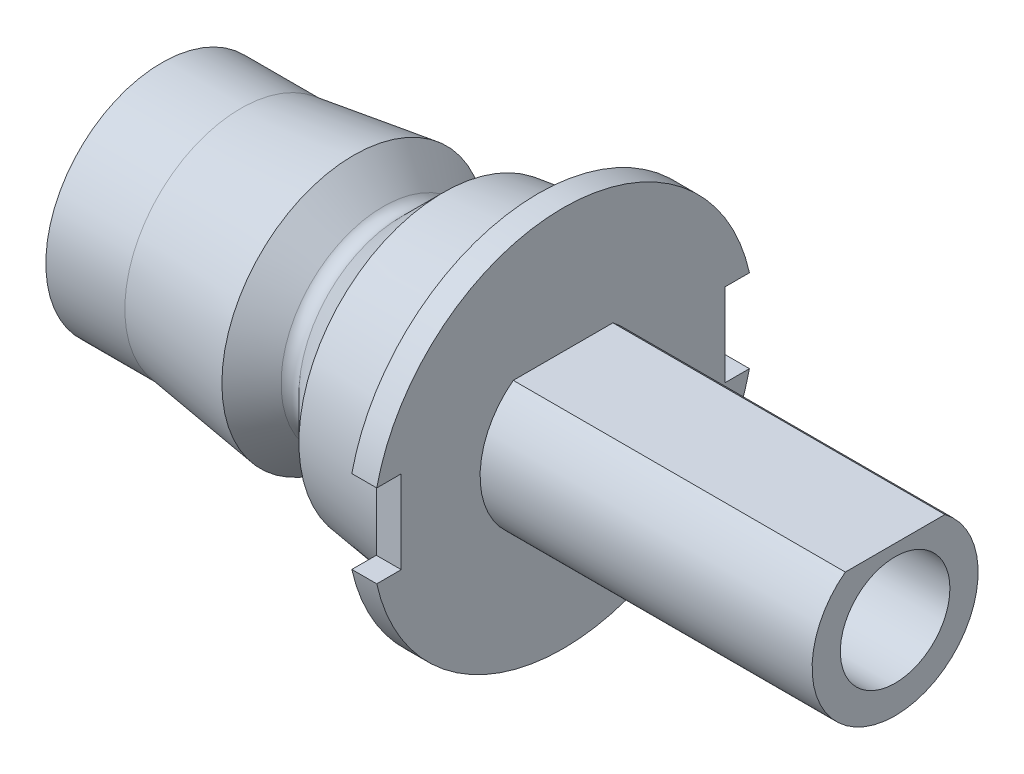
SolidWorks part; units mm, degrees
ref_plane "Front Plane" through (0, 0, 0) normal (0, 0, 1) x (1, 0, 0)
ref_plane "Top Plane" through (0, 0, 0) normal (0, 1, 0) x (1, 0, 0)
ref_plane "Right Plane" through (0, 0, 0) normal (1, 0, 0) x (0, 0, -1)
sketch "Sketch1" plane through (0, 0, 0) normal (0, 0, 1) x (1, 0, 0)
  line L0 (0, 0) -> (0, 6.982)
  line L1 (0, 6.982) -> (4.76, 6.982)
  line L2 (4.76, 6.982) -> (11.56, 7.9377)
  line L3 (11.56, 7.9377) -> (13.3431, 6.1545)
  line L4 (11.56, 7.9377) -> (23.1675, 9.569) construction
  line L5 (16.96, 8.6966) -> (22.6765, 9.5)
  line L6 (4.76, 6.982) -> (7.8351, 6.982) construction
  line L7 (11.56, 7.9377) -> (15.4875, 7.9377) construction
  line L8 (16.96, 8.6966) -> (14.4179, 6.1545)
  line L9 (16.96, 8.6966) -> (14.3792, 8.6966) construction
  line L10 (14.4179, 6.1545) -> (13.8805, 6.6919) construction
  line L11 (13.8805, 6.6919) -> (13.3431, 6.1545) construction
  line L12 (22.6765, 9.5) -> (22.6765, 11.5)
  line L13 (22.6765, 11.5) -> (24.1765, 11.5)
  line L14 (24.1765, 11.5) -> (24.1765, 0)
  line L15 (0, 0) -> (31.0457, 0) construction
  line L16 (24.1765, 0) -> (0, 0)
  line L17 (0, 0) -> (71.6905, 0) construction
  arc A0 (14.4179, 6.1545) -> (13.3431, 6.1545) centre (13.8805, 6.6919) cw
  point P17 (44.4459, 0)
  point P21 (71.6905, 0)
  dimension "D1" = 6.982
  dimension "D2" = 4.76
  dimension "D3" = 11.56
  dimension "D4" = 16.96
  dimension "D5" = 8
  dimension "D6" = 45
  dimension "D7" = 45
  dimension "D8" = 0.76
  dimension "D9" = 9.5
  dimension "D10" = 11.5
  dimension "D11" = 1.5
revolve "Revolve3" add sketch "Sketch1" angle 360 about L16
sketch "Sketch3" plane through (24.1765, 0, 0) normal (1, 0, 0) x (0, 0, -1)
  line L0 (0, 0) -> (15.7286, 0) construction
  line L1 (0, 0) -> (-16.4314, 0) construction
  line L2 (-11.75, 2.5) -> (-9.75, 2.5)
  line L3 (9.75, 2.5) -> (11.75, 2.5)
  line L4 (9.75, 2.5) -> (9.75, -2.5)
  line L5 (9.75, -2.5) -> (11.75, -2.5)
  line L6 (11.75, 2.5) -> (11.75, -2.5)
  line L7 (-11.75, 2.5) -> (-11.75, -2.5)
  line L8 (-11.75, -2.5) -> (-9.75, -2.5)
  line L9 (-9.75, 2.5) -> (-9.75, -2.5)
  point P8 (11.75, 0)
  point P13 (-9.75, 0)
  dimension "D1" = 2
  dimension "D2" = 5
  dimension "D3" = 9.75
  dimension "D4" = 2
  dimension "D5" = 9.75
extrude "Cut-Extrude6" cut sketch "Sketch3" against normal through all
sketch "Sketch4" plane through (24.1765, 0, 0) normal (1, 0, 0) x (0, 0, -1)
  line L0 (-3, 4) -> (3, 4)
  arc A0 (-3, 4) -> (3, 4) centre (0, 0) ccw
  dimension "D1" = 10
  dimension "D2" = 4
extrude "Boss-Extrude4" add sketch "Sketch4" along normal blind 20
sketch "Sketch2" plane through (0, 0, 0) normal (1, 0, 0) x (0, 0, -1)
  circle A0 centre (0, 0) radius 3.3
  dimension "D1" = 6.6
extrude "Cut-Extrude7" cut sketch "Sketch2" along normal through all
